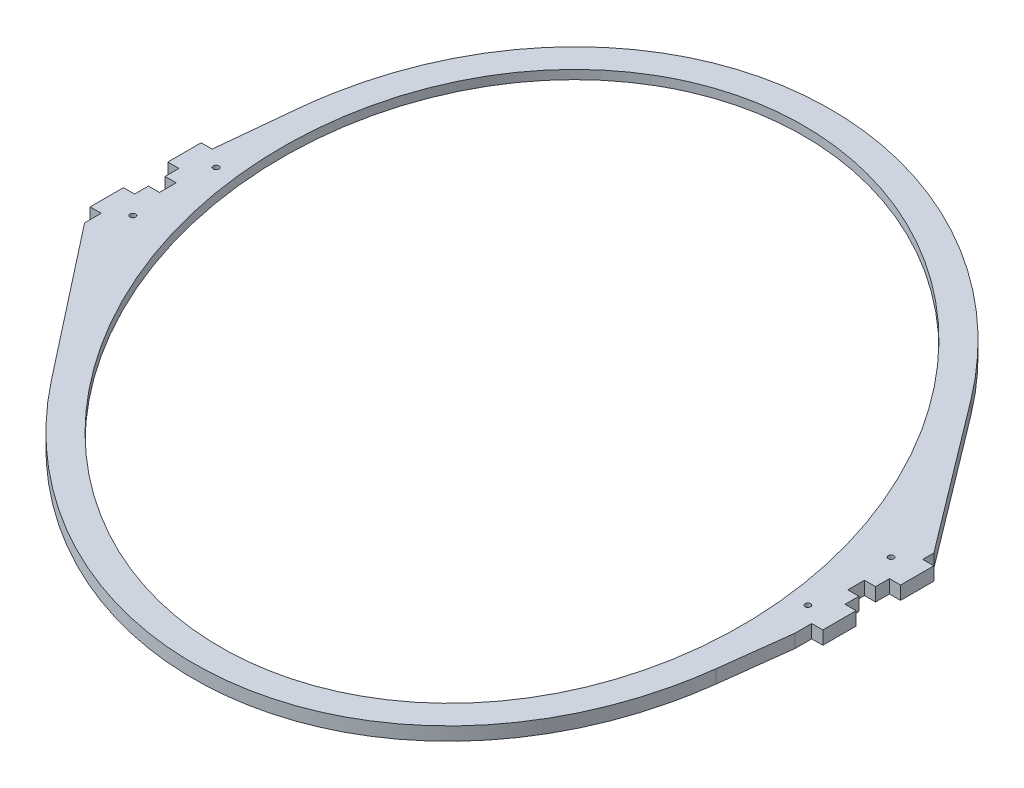
SolidWorks part; units mm, degrees
ref_plane "Front Plane" through (0, 0, 0) normal (0, 0, 1) x (1, 0, 0)
ref_plane "Top Plane" through (0, 0, 0) normal (0, 1, 0) x (1, 0, 0)
ref_plane "Right Plane" through (0, 0, 0) normal (1, 0, 0) x (0, 0, -1)
sketch "Sketch1" plane through (0, 0, 0) normal (0, 1, 0) x (1, 0, 0)
  line L0 (0, 520.2694) -> (0, -520.3963) construction
  line L1 (-478.2136, 0) -> (435.079, 0) construction
  line L2 (-270, 0) -> (-270, 60) construction
  line L3 (-270, 60) -> (-290, 60) construction
  line L4 (-290, 60) -> (-290, -60) construction
  line L5 (-320, 50) -> (-320, 51)
  line L6 (-330, -20) -> (-330, -50)
  line L7 (-320, -50) -> (-320, -65)
  line L8 (-330, -50) -> (-320, -50)
  line L9 (290, 60) -> (290, -60) construction
  line L10 (-320, -20) -> (-330, -20)
  line L11 (-320, 0) -> (-320, -20)
  line L12 (-320, 0) -> (-320, 20)
  line L13 (-320, 20) -> (-330, 20)
  line L14 (-330, 20) -> (-330, 50)
  line L15 (-330, 50) -> (-320, 50)
  line L16 (-320, 51) -> (-313.0913, 120.0927)
  line L17 (-320, -65) -> (-212.2821, -202.5885)
  line L19 (-290, 60) -> (-290, -60) construction
  line L29 (-177.5, 307.439) -> (177.5, -307.439) construction
  line L30 (320, 0) -> (320, 20)
  line L31 (320, 20) -> (330, 20)
  line L32 (330, 20) -> (330, 50)
  line L33 (330, 50) -> (320, 50)
  line L34 (320, 50) -> (320, 60)
  line L35 (320, 0) -> (320, -20)
  line L36 (320, -20) -> (330, -20)
  line L37 (330, -20) -> (330, -50)
  line L38 (330, -50) -> (320, -50)
  line L39 (320, -50) -> (320, -65)
  line L40 (320, -65) -> (312.1702, -128.3352)
  line L41 (320, 60) -> (217.5479, 195.7385)
  ellipse E0 centre (0, 0) end of major axis (-190, 329.0897) minor radius 290 (217.5479, 195.7385) -> (-313.0913, 120.0927) ccw
  ellipse E1 centre (0, 0) end of major axis (0, 380) minor radius 290 construction
  ellipse E3 centre (0, 0) end of major axis (-177.5, 307.439) minor radius 265
  ellipse E7 centre (0, 0) end of major axis (-190, 329.0897) minor radius 290 (-212.2821, -202.5885) -> (312.1702, -128.3352) ccw
  point P27 (290, 0)
  point P32 (-290, 0)
  point P42 (290, 0)
  dimension "D2" = 10
  dimension "D3" = 580
  dimension "D4" = 760
  dimension "D5" = 20
  dimension "D6" = 10
  dimension "D7" = 60
  dimension "D8" = 10
  dimension "D9" = 320
  dimension "D10" = 30
  dimension "D11" = 710
  dimension "D12" = 530
  dimension "D13" = 760
  dimension "D14" = 580
  dimension "D15" = 30
  dimension "D16" = 30
  dimension "D17" = 20
  dimension "D18" = 20
  dimension "D19" = 15
  dimension "D20" = 10
  dimension "D21" = 1
extrude "Boss-Extrude1" add sketch "Sketch1" along normal blind 12
sketch "Sketch2" plane through (0, 12, 0) normal (0, 1, 0) x (1, 0, 0)
  line L0 (0, 0) -> (451.8605, 0) construction
  line L1 (320, -20) -> (320, 20) construction
  line L2 (320, -7.5) -> (310, -7.5)
  line L3 (320, -7.5) -> (320, 7.5)
  line L4 (320, 7.5) -> (310, 7.5)
  line L5 (310, -7.5) -> (310, 7.5)
  line L6 (0, 0) -> (0, 314.2562) construction
  line L7 (-310, -7.5) -> (-310, 7.5)
  line L8 (-320, 7.5) -> (-310, 7.5)
  line L9 (-320, -7.5) -> (-320, 7.5)
  line L10 (-320, -7.5) -> (-310, -7.5)
  point P3 (-320, 0)
  point P10 (310, 0)
  point P11 (320, 0)
  point P13 (-310, 0)
  dimension "D1" = 15
  dimension "D2" = 10
extrude "Cut-Extrude1" cut sketch "Sketch2" against normal blind 12
hole_wizard "Ø5.0 (5) Diameter Hole2" positions "Sketch5" profile "Sketch6" hole size "Ø5.0" standard "ANSI Metric"
sketch "Sketch5" plane through (0, 12, 0) normal (0, 1, 0) x (1, 0, 0)
  point P0 (304, 37.5)
  point P3 (304, -37.5)
  point P6 (-304, -37.5)
  point P9 (-304, 37.5)
sketch "Sketch6" plane through (304, 12, -37.5) normal (1, 0, 0) x (0, 0, 1)
  line L0 (0, 0) -> (0, 26.5022)
  line L1 (0, 26.5022) -> (2.5, 25)
  line L2 (2.5, 25) -> (2.5, 0)
  line L3 (2.5, 0) -> (0, 0)
  line L4 (0, 26.5022) -> (-2.5, 25) construction
  line L5 (0, -6.35) -> (0, 107.95) construction
  dimension "Hole Dia." = 5
  dimension "Hole Depth" = 25
  dimension "Drill Angle" = 118
sketch "Sketch9" plane through (0, 0, 0) normal (0, -1, 0) x (1, 0, 0)
  line L0 (0, 0) -> (177.5, 307.439) construction
  line L1 (0, 0) -> (229.4967, -132.5) construction
  ellipse E0 centre (0, 0) end of major axis (-182.5, -316.0993) minor radius 275
  ellipse E1 centre (0, 0) end of major axis (-177.5, -307.439) minor radius 265 construction
  dimension "D1" = 10
  dimension "D2" = 10
extrude "Cut-Extrude4" cut sketch "Sketch9" against normal blind 4
sketch "Sketch7" plane through (0, 12, 0) normal (0, 1, 0) x (1, 0, 0)
  line L0 (0, 0) -> (-211.3091, 453.1539)
  line L1 (0, 0) -> (211.3091, -453.1539)
  line L2 (0, 0) -> (0, 490.0448) construction
  arc A0 (-211.3091, 453.1539) -> (211.3091, -453.1539) centre (0, 0) ccw
  dimension "D2" = 500
  dimension "D1" = 25
extrude "Cut-Extrude2" [suppressed] cut sketch "Sketch7" against normal blind 12
sketch "Sketch8" plane through (0, 12, 0) normal (0, 1, 0) x (1, 0, 0)
  line L0 (0, 0) -> (-211.3091, 453.1539)
  line L1 (0, 0) -> (211.3091, -453.1539)
  line L2 (0, 0) -> (0, 207.06) construction
  arc A0 (-211.3091, 453.1539) -> (211.3091, -453.1539) centre (0, 0) cw
  dimension "D2" = 500
  dimension "D1" = 25
extrude "Cut-Extrude3" [suppressed] cut sketch "Sketch8" against normal blind 12
